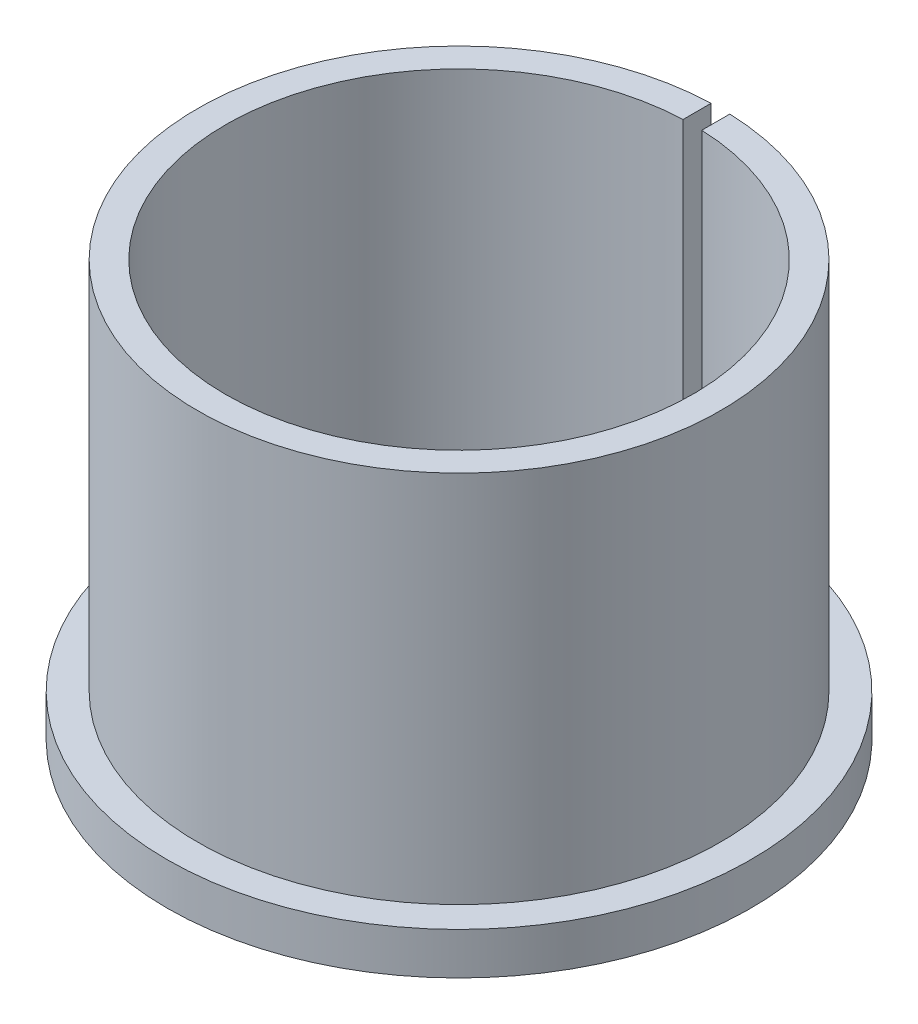
SolidWorks part; units mm, degrees
ref_plane "Plan de face" through (0, 0, 0) normal (0, 0, 1) x (1, 0, 0)
ref_plane "Plan de dessus" through (0, 0, 0) normal (0, 1, 0) x (1, 0, 0)
ref_plane "Plan de droite" through (0, 0, 0) normal (1, 0, 0) x (0, 0, -1)
sketch "Esquisse1" plane through (0, 0, 0) normal (1, 0, 0) x (0, 0, -1)
  line L0 (0, 0) -> (0, 44.5) construction
  line L1 (25, 44.5) -> (25, 0)
  line L2 (25, 0) -> (31.25, 0)
  line L3 (31.25, 0) -> (31.25, 4.5)
  line L4 (31.25, 4.5) -> (28, 4.5)
  line L5 (28, 4.5) -> (28, 44.5)
  line L6 (28, 44.5) -> (25, 44.5)
  dimension "D1" = 44.5
  dimension "D2" = 25
  dimension "D3" = 31.25
  dimension "D4" = 4.5
  dimension "D5" = 28
revolve "Révolution1" add sketch "Esquisse1" angle 360 about L0
sketch "Esquisse2" plane through (0, 0, 0) normal (0, 0, 1) x (1, 0, 0)
  line L0 (25, 44.5) -> (-25, 44.5) construction
  line L1 (-1, 0) -> (1, 0)
  line L2 (-1, 0) -> (-1, 44.5)
  line L3 (-1, 44.5) -> (1, 44.5)
  line L4 (1, 0) -> (1, 44.5)
  line L5 (-1, 0) -> (1, 44.5) construction
  line L6 (-1, 44.5) -> (1, 0) construction
  line L7 (-31.25, 0) -> (31.25, 0) construction
  line L8 (0, 0) -> (0, 44.5) construction
  point P0 (0, 22.25)
  dimension "D1" = 2
extrude "Enlèv. mat.-Extru.1" cut sketch "Esquisse2" against normal through all
equation "\"D2@Esquisse1\"=50/2"
equation "\"D3@Esquisse1\"=62.5/2"
equation "\"D5@Esquisse1\"=56/2"
